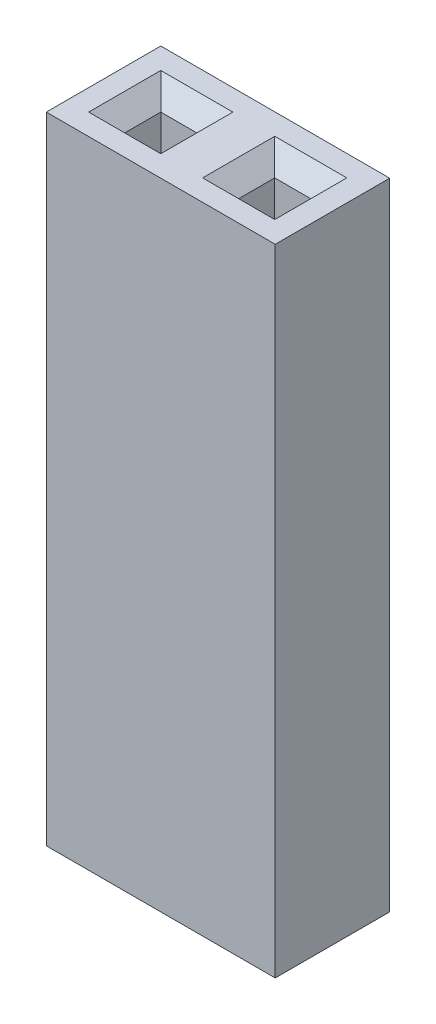
SolidWorks part; units mm, degrees
ref_plane "Спереди" through (0, 0, 0) normal (0, 0, 1) x (1, 0, 0)
ref_plane "Сверху" through (0, 0, 0) normal (0, 1, 0) x (1, 0, 0)
ref_plane "Справа" through (0, 0, 0) normal (1, 0, 0) x (0, 0, -1)
sketch "Эскиз1" plane through (0, 0, 0) normal (0, 1, 0) x (1, 0, 0)
  line L1 (0, 0) -> (5.08, 0)
  line L2 (0, 0) -> (0, 2.54)
  line L3 (0, 2.54) -> (5.08, 2.54)
  line L4 (5.08, 0) -> (5.08, 2.54)
  dimension "D1" = 2.54
  dimension "D2" = 5.08
extrude "Бобышка-Вытянуть1" add sketch "Эскиз1" along normal blind 14.1
sketch "Эскиз2" plane through (0, 14.1, 0) normal (0, 1, 0) x (1, 0, 0)
  line L0 (0, 2.54) -> (0, 0) construction
  line L5 (0.87, 0.87) -> (1.67, 0.87)
  line L6 (0.87, 0.87) -> (0.87, 1.67)
  line L7 (0.87, 1.67) -> (1.67, 1.67)
  line L8 (1.67, 0.87) -> (1.67, 1.67)
  line L9 (0.87, 0.87) -> (1.67, 1.67) construction
  line L10 (0.87, 1.67) -> (1.67, 0.87) construction
  line L12 (5.08, 2.54) -> (0, 2.54) construction
  line L13 (0.47, 0.47) -> (2.07, 0.47)
  line L14 (0.47, 0.47) -> (0.47, 2.07)
  line L15 (0.47, 2.07) -> (2.07, 2.07)
  line L16 (2.07, 0.47) -> (2.07, 2.07)
  line L17 (0.47, 0.47) -> (2.07, 2.07) construction
  line L18 (0.47, 2.07) -> (2.07, 0.47) construction
  line L19 (3.41, 0.87) -> (4.21, 0.87)
  line L20 (3.41, 0.87) -> (3.41, 1.67)
  line L21 (3.41, 1.67) -> (4.21, 1.67)
  line L22 (4.21, 0.87) -> (4.21, 1.67)
  line L23 (3.41, 0.87) -> (4.21, 1.67) construction
  line L24 (3.41, 1.67) -> (4.21, 0.87) construction
  line L25 (3.01, 0.47) -> (4.61, 0.47)
  line L26 (3.01, 0.47) -> (3.01, 2.07)
  line L27 (3.01, 2.07) -> (4.61, 2.07)
  line L28 (4.61, 0.47) -> (4.61, 2.07)
  line L29 (3.01, 0.47) -> (4.61, 2.07) construction
  line L30 (3.01, 2.07) -> (4.61, 0.47) construction
  line L31 (5.08, 0) -> (5.08, 2.54) construction
  point P0 (1.27, 1.27)
  point P12 (1.27, 1.27)
  point P21 (3.81, 1.27)
  point P26 (3.81, 1.27)
  dimension "D1" = 1.27
  dimension "D2" = 1.27
  dimension "D3" = 0.8
  dimension "D4" = 0.8
  dimension "D5" = 1.6
  dimension "D6" = 1.6
  dimension "D7" = 0.8
  dimension "D8" = 0.8
  dimension "D9" = 1.6
  dimension "D10" = 1.6
  dimension "D11" = 1.27
  dimension "D12" = 1.27
sketch "Эскиз5" plane through (0, 14.1, 0) normal (0, 1, 0) x (1, 0, 0)
  line L0 (0.87, 0.87) -> (1.67, 0.87)
  line L1 (0.87, 0.87) -> (0.87, 1.67)
  line L2 (0.87, 1.67) -> (1.67, 1.67)
  line L3 (1.67, 0.87) -> (1.67, 1.67)
  line L4 (0.87, 0.87) -> (1.67, 1.67) construction
  line L5 (0.87, 1.67) -> (1.67, 0.87) construction
  line L6 (0.47, 0.47) -> (2.07, 0.47)
  line L7 (0.47, 0.47) -> (0.47, 2.07)
  line L8 (0.47, 2.07) -> (2.07, 2.07)
  line L9 (2.07, 0.47) -> (2.07, 2.07)
  line L10 (0.47, 0.47) -> (2.07, 2.07) construction
  line L11 (0.47, 2.07) -> (2.07, 0.47) construction
  line L12 (3.3989, 0.87) -> (4.1989, 0.87)
  line L13 (3.3989, 0.87) -> (3.3989, 1.67)
  line L14 (3.3989, 1.67) -> (4.1989, 1.67)
  line L15 (4.1989, 0.87) -> (4.1989, 1.67)
  line L16 (3.3989, 0.87) -> (4.1989, 1.67) construction
  line L17 (3.3989, 1.67) -> (4.1989, 0.87) construction
  line L18 (2.9989, 0.47) -> (4.5989, 0.47)
  line L19 (2.9989, 0.47) -> (2.9989, 2.07)
  line L20 (2.9989, 2.07) -> (4.5989, 2.07)
  line L21 (4.5989, 0.47) -> (4.5989, 2.07)
  line L22 (2.9989, 0.47) -> (4.5989, 2.07) construction
  line L23 (2.9989, 2.07) -> (4.5989, 0.47) construction
  line L24 (5.08, 2.54) -> (0, 2.54) construction
  line L25 (0, 2.54) -> (0, 0) construction
  line L26 (5.08, 0) -> (5.08, 2.54) construction
  point P0 (1.27, 1.27)
  point P5 (1.27, 1.27)
  point P10 (3.7989, 1.27)
  point P15 (3.7989, 1.27)
  dimension "D1" = 0.8
  dimension "D2" = 0.8
  dimension "D3" = 1.6
  dimension "D4" = 0.8
  dimension "D5" = 0.8
  dimension "D6" = 1.6
  dimension "D7" = 1.27
  dimension "D8" = 1.27
  dimension "D9" = 1.27
  dimension "D10" = 1.2811
extrude "Вырез-Вытянуть5" cut sketch "Эскиз5" against normal blind 10 contours L0 L3 L2 L1 | L12 L15 L14 L13
chamfer "Фаска5" distance 0.4 8 edges at (3.7989, 14.1, -1.67) (4.1989, 14.1, -1.27) (3.7989, 14.1, -0.87) (3.3989, 14.1, -1.27) (0.87, 14.1, -1.27) (1.27, 14.1, -1.67) (1.67, 14.1, -1.27) (1.27, 14.1, -0.87)
extrude "Вырез-Вытянуть2" cut sketch "Эскиз2" against normal blind 10 contours L5 L8 L7 L6 | L19 L22 L21 L20
